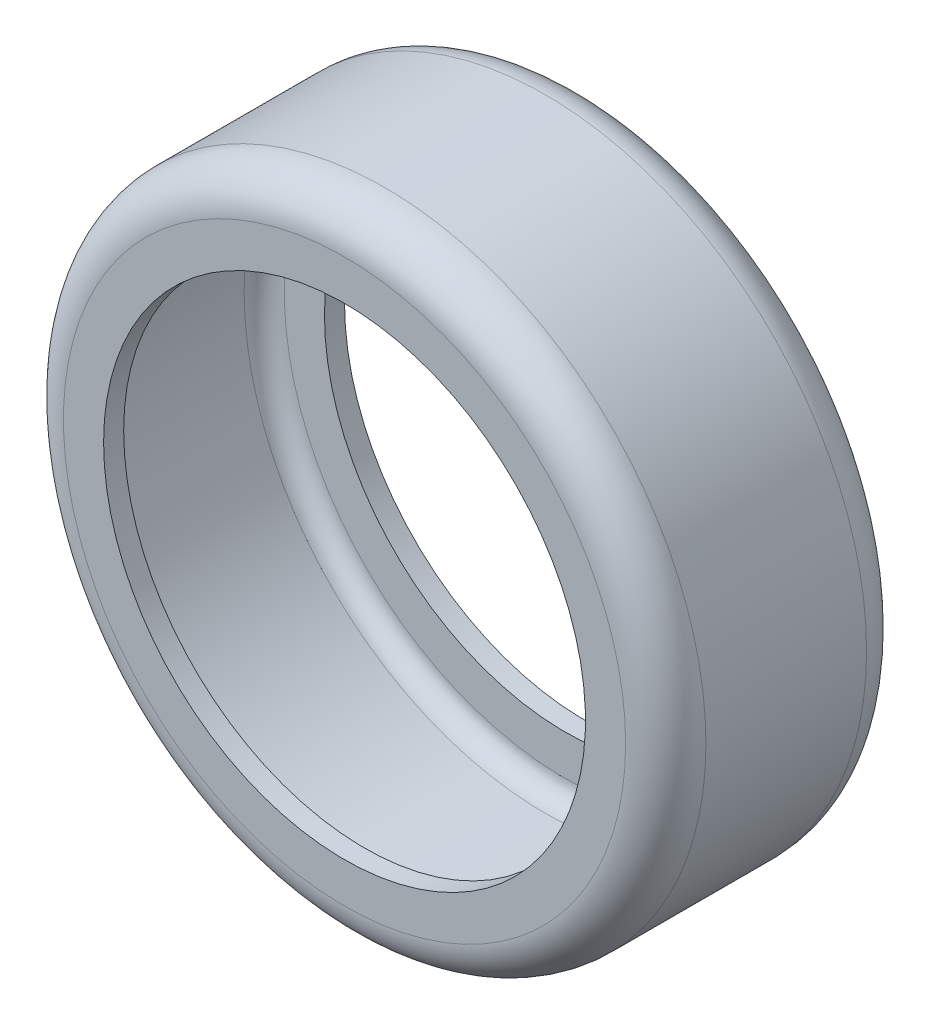
SolidWorks part; units mm, degrees
material "SBR"
ref_plane "Front Plane" through (0, 0, 0) normal (0, 0, 1) x (1, 0, 0)
ref_plane "Top Plane" through (0, 0, 0) normal (0, 1, 0) x (1, 0, 0)
ref_plane "Right Plane" through (0, 0, 0) normal (1, 0, 0) x (0, 0, -1)
sketch "Sketch2" plane through (0, 0, 0) normal (0, 0, 1) x (1, 0, 0)
  circle A0 centre (0, 0) radius 76.2
  circle A1 centre (0, 0) radius 101.6
  dimension "D1" = 152.4
  dimension "D2" = 203.2
extrude "Boss-Extrude1" add sketch "Sketch2" along normal mid plane 76.2
fillet "Fillet2" radius 12.7 2 edges at (101.6, 0, -38.1) (101.6, 0, 38.1)
shell "Shell1" thickness 6.35
